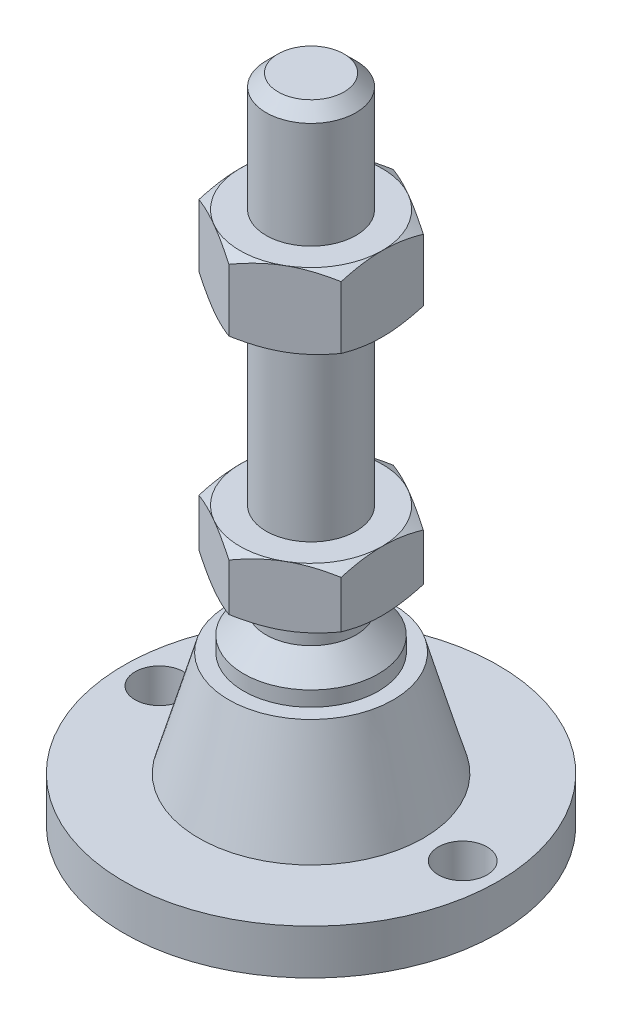
SolidWorks part; units mm, degrees
ref_plane "Спереди" through (0, 0, 0) normal (0, 0, 1) x (1, 0, 0)
ref_plane "Сверху" through (0, 0, 0) normal (0, 1, 0) x (1, 0, 0)
ref_plane "Справа" through (0, 0, 0) normal (1, 0, 0) x (0, 0, -1)
sketch "Эскиз1" plane through (0, 0, 0) normal (0, 0, 1) x (1, 0, 0)
  line L0 (0, 0) -> (-25, 0)
  line L3 (-25, 0) -> (-25, 6)
  line L12 (-6, 37) -> (-6, 85.4)
  line L13 (-6, 85.4) -> (-4.4, 87)
  line L14 (-4.4, 87) -> (0, 87)
  line L15 (0, 87) -> (0, 0) construction
  line L16 (-25, 6) -> (-15, 6)
  line L17 (0, 0) -> (0, 87)
  line L18 (0, 0) -> (0, -7.9595) construction
  line L19 (-6, 37) -> (-6, 29)
  line L21 (-9, 20) -> (-11, 20)
  line L22 (-15, 6) -> (-11, 20)
  line L23 (-9, 20) -> (-9, 22)
  line L24 (-9, 22) -> (-6, 25)
  line L25 (-6, 25) -> (-6, 29)
  line L26 (-6, 37) -> (0, 37) construction
  point P8 (-6, 61.2)
revolve "Повернуть1" add sketch "Эскиз1" angle 360 about L17
ref_plane "Плоскость2" through (0, 29, 0) normal (0, 1, 0) x (1, 0, 0)
sketch "Эскиз2" plane through (0, 29, 0) normal (0, 1, 0) x (1, 0, 0)
  line L1 (0, 10.9697) -> (-9.5, 5.4848)
  line L2 (-9.5, 5.4848) -> (-9.5, -5.4848)
  line L3 (-9.5, -5.4848) -> (0, -10.9697)
  line L4 (0, -10.9697) -> (9.5, -5.4848)
  line L5 (9.5, -5.4848) -> (9.5, 5.4848)
  line L6 (9.5, 5.4848) -> (0, 10.9697)
  circle A0 centre (0, 0) radius 9.5 construction
  dimension "D1" = 19
extrude "Бобышка-Вытянуть1" add sketch "Эскиз2" along normal up to vertex (8 mm away) up to point (-6, 37, 0)
ref_plane "Плоскость1" through (0, 61.2, 0) normal (0, 1, 0) x (1, 0, 0)
sketch "Эскиз3" plane through (0, 61.2, 0) normal (0, 1, 0) x (1, 0, 0)
  line L6 (9.5, 5.4848) -> (0, 10.9697)
  line L7 (0, 10.9697) -> (-9.5, 5.4848)
  line L8 (-9.5, 5.4848) -> (-9.5, -5.4848)
  line L9 (-9.5, -5.4848) -> (0, -10.9697)
  line L10 (0, -10.9697) -> (9.5, -5.4848)
  line L11 (9.5, -5.4848) -> (9.5, 5.4848)
  line L12 (9.5, 5.4848) -> (0, 10.9697)
  line L13 (0, 10.9697) -> (-9.5, 5.4848)
  line L14 (-9.5, 5.4848) -> (-9.5, -5.4848)
  line L15 (-9.5, -5.4848) -> (0, -10.9697)
  line L16 (0, -10.9697) -> (9.5, -5.4848)
  line L17 (9.5, -5.4848) -> (9.5, 5.4848)
  dimension "D1" = 0
extrude "Бобышка-Вытянуть2" add sketch "Эскиз3" along normal blind 10
sketch "Эскиз4" plane through (0, 0, 0) normal (0, 0, 1) x (1, 0, 0)
  line L0 (-9.5, 71.2) -> (-18.1603, 66.2)
  line L1 (-18.1603, 66.2) -> (-18.1603, 71.2)
  line L2 (-18.1603, 71.2) -> (-9.5, 71.2)
  line L3 (-18.1603, 66.2) -> (-9.5, 61.2)
  line L4 (50, 61.2) -> (-50, 61.2) construction
  line L5 (-9.5, 61.2) -> (-18.1603, 61.2)
  line L6 (-18.1603, 61.2) -> (-18.1603, 66.2)
  line L7 (-9.5, 71.2) -> (-9.5, 61.2) construction
  line L8 (-9.5, 37) -> (-16.4282, 37)
  line L9 (-16.4282, 37) -> (-16.4282, 33)
  line L10 (-16.4282, 33) -> (-9.5, 37)
  line L11 (-9.5, 29) -> (-16.4282, 33)
  line L12 (-16.4282, 33) -> (-16.4282, 29)
  line L13 (-16.4282, 29) -> (-9.5, 29)
  line L14 (0, 87) -> (0, 96.3793) construction
  line L15 (50, 29) -> (-50, 29) construction
  dimension "D1" = 30
  dimension "D2" = 30
revolve "Вырез-Повернуть2" cut sketch "Эскиз4" angle 360 about L14
sketch "Эскиз5" plane through (0, 6, 0) normal (0, 1, 0) x (1, 0, 0)
  line L0 (20.25, 0) -> (-20.25, 0) construction
  circle A0 centre (-20.25, 0) radius 3.25
  circle A1 centre (20.25, 0) radius 3.25
  circle A2 centre (0, 0) radius 25 construction
  dimension "D1" = 6.5
  dimension "D2" = 1.5
extrude "Вырез-Вытянуть1" cut sketch "Эскиз5" against normal through all
equation "\"D13@Эскиз1\"=\"D12@Эскиз1\"/2"
